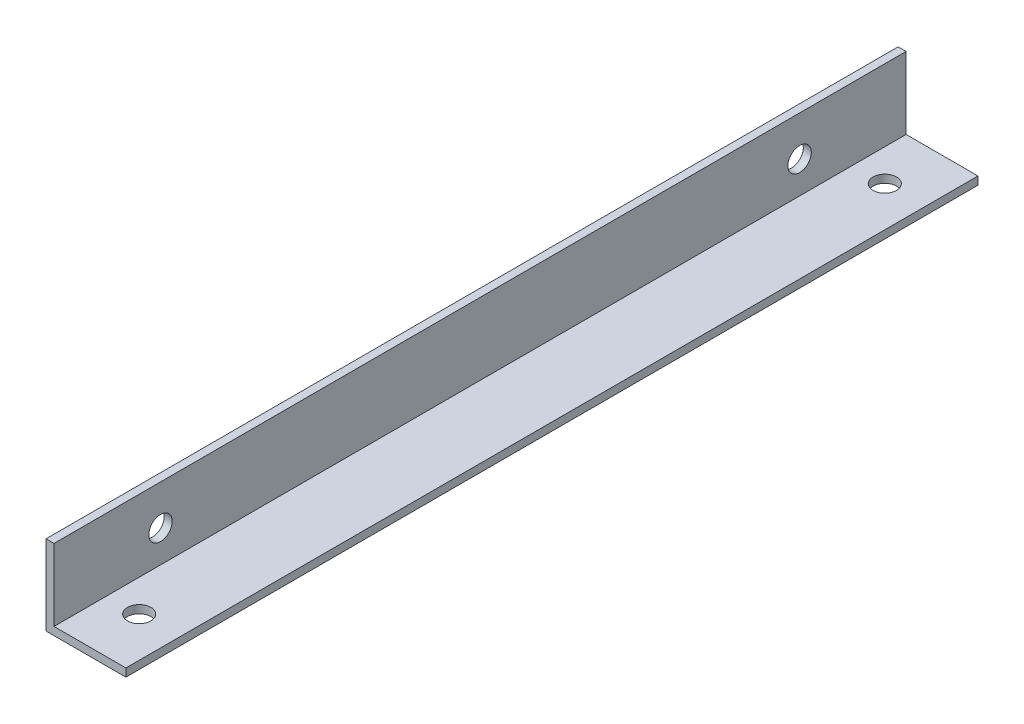
SolidWorks part; units mm, degrees
ref_plane "正面" through (0, 0, 0) normal (0, 0, 1) x (1, 0, 0)
ref_plane "平面" through (0, 0, 0) normal (0, 1, 0) x (1, 0, 0)
ref_plane "右側面" through (0, 0, 0) normal (1, 0, 0) x (0, 0, -1)
sketch "ｽｹｯﾁ1" plane through (0, 0, 0) normal (0, 0, 1) x (1, 0, 0)
  line L0 (0, 0) -> (0, 15)
  line L1 (0, 15) -> (1.5, 15)
  line L2 (1.5, 15) -> (1.5, 1.5)
  line L3 (1.5, 1.5) -> (15, 1.5)
  line L4 (15, 1.5) -> (15, 0)
  line L5 (15, 0) -> (0, 0)
  dimension "D1" = 15
  dimension "D2" = 15
  dimension "D3" = 1.5
  dimension "D4" = 1.5
extrude "ﾎﾞｽ - 押し出し1" add sketch "ｽｹｯﾁ1" along normal blind 160
sketch "ｽｹｯﾁ2" plane through (0, 0, 0) normal (-1, 0, 0) x (0, 0, 1)
  line L0 (160, 7.5) -> (140, 7.5)
  line L1 (160, 15) -> (160, 0) construction
  line L2 (0, 7.5) -> (20, 7.5)
  line L3 (0, 15) -> (0, 0) construction
  circle A0 centre (20, 7.5) radius 2.2
  circle A1 centre (140, 7.5) radius 2.2
  dimension "D2" = 4.4
  dimension "D4" = 4.4
  dimension "D1" = 20
  dimension "D3" = 20
extrude "ｶｯﾄ - 押し出し1" cut sketch "ｽｹｯﾁ2" against normal through all
sketch "ｽｹｯﾁ3" plane through (0, 0, 0) normal (0, -1, 0) x (-1, 0, 0)
  line L0 (-7.5, 0) -> (-7.5, -10)
  line L1 (0, 0) -> (-15, 0) construction
  line L2 (-7.5, -160) -> (-7.5, -150)
  line L3 (0, -160) -> (-15, -160) construction
  circle A0 centre (-7.5, -10) radius 2.2
  circle A1 centre (-7.5, -150) radius 2.2
  dimension "D3" = 4.4
  dimension "D4" = 4.4
  dimension "D1" = 10
  dimension "D2" = 10
extrude "ｶｯﾄ - 押し出し2" cut sketch "ｽｹｯﾁ3" against normal blind 160
